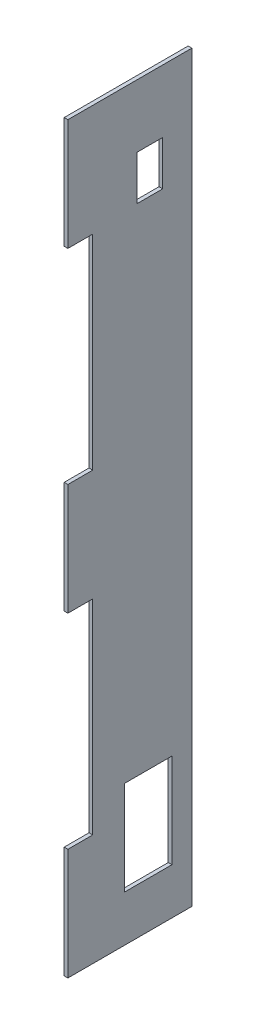
SolidWorks part; units mm, degrees
ref_plane "Front Plane" through (0, 0, 0) normal (0, 0, 1) x (1, 0, 0)
ref_plane "Top Plane" through (0, 0, 0) normal (0, 1, 0) x (1, 0, 0)
ref_plane "Right Plane" through (0, 0, 0) normal (1, 0, 0) x (0, 0, -1)
sketch "Sketch1" plane through (0, 0, 0) normal (0, 1, 0) x (1, 0, 0)
  line L1 (-0.75, 25) -> (0.75, 25)
  line L2 (-0.75, 25) -> (-0.75, -25)
  line L3 (-0.75, -25) -> (0.75, -25)
  line L4 (0.75, 25) -> (0.75, -25)
  line L5 (-0.75, 25) -> (0.75, -25) construction
  line L6 (-0.75, -25) -> (0.75, 25) construction
  point P0 (0, 0)
  dimension "D1" = 50
  dimension "D2" = 1.5
extrude "Boss-Extrude1" add sketch "Sketch1" along normal mid plane 300
sketch "Sketch2" plane through (-0.75, 0, 0) normal (-1, 0, 0) x (0, 0, 1)
  line L0 (-25, 150) -> (25, 150) construction
  line L1 (25, 105) -> (15, 105)
  line L2 (25, 105) -> (25, 22.5)
  line L3 (25, 22.5) -> (15, 22.5)
  line L4 (15, 105) -> (15, 22.5)
  line L5 (25, 150) -> (25, -150) construction
  line L6 (0, 0) -> (25, 0) construction
  line L7 (25, -105) -> (25, -22.5)
  line L8 (25, -22.5) -> (15, -22.5)
  line L9 (15, -105) -> (15, -22.5)
  line L10 (25, -105) -> (15, -105)
  dimension "D1" = 45
  dimension "D2" = 10
  dimension "D3" = 45
extrude "Cut-Extrude1" cut sketch "Sketch2" against normal through all
sketch "Sketch3" plane through (-0.75, 0, 0) normal (-1, 0, 0) x (0, 0, 1)
  line L1 (2.1285, -93.415) -> (-16.9891, -93.415)
  line L2 (2.1285, -93.415) -> (2.1285, -131.3885)
  line L3 (2.1285, -131.3885) -> (-16.9891, -131.3885)
  line L4 (-16.9891, -93.415) -> (-16.9891, -131.3885)
extrude "PowerConn" cut sketch "Sketch3" against normal through all
sketch "Sketch4" plane through (-0.75, 0, 0) normal (-1, 0, 0) x (0, 0, 1)
  line L1 (-2.9575, 124.6559) -> (-13.2547, 124.6559)
  line L2 (-2.9575, 124.6559) -> (-2.9575, 106.6975)
  line L3 (-2.9575, 106.6975) -> (-13.2547, 106.6975)
  line L4 (-13.2547, 124.6559) -> (-13.2547, 106.6975)
extrude "UsbConn" cut sketch "Sketch4" against normal through all
